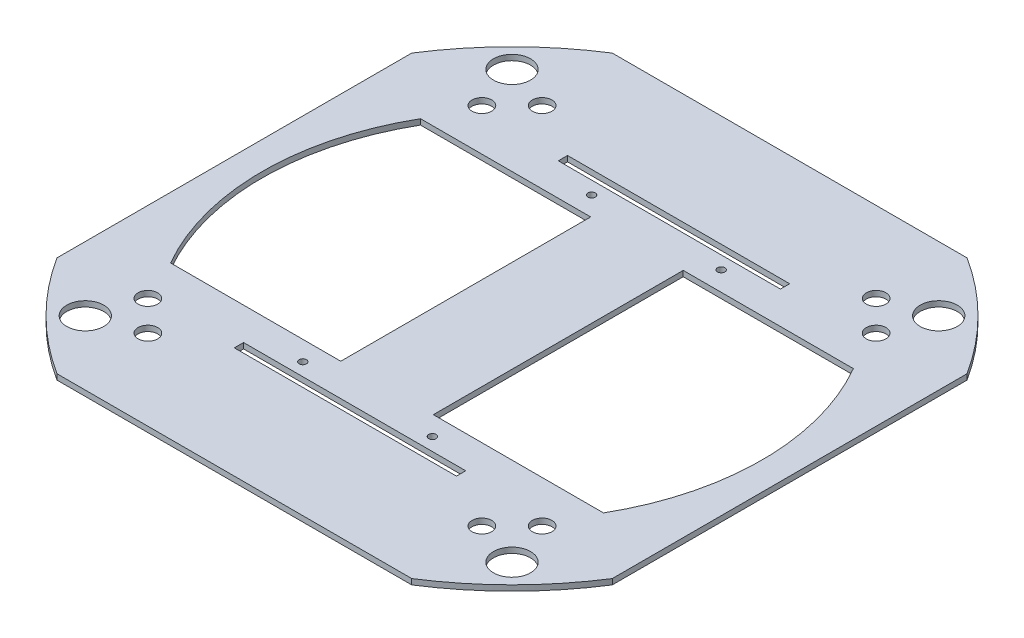
SolidWorks part; units mm, degrees
material "Hexcel AS4C (3000 丝)"
ref_plane "Front" through (0, 0, 0) normal (0, 0, 1) x (1, 0, 0)
ref_plane "Top" through (0, 0, 0) normal (0, 1, 0) x (1, 0, 0)
ref_plane "Right" through (0, 0, 0) normal (1, 0, 0) x (0, 0, -1)
sketch "草图3" plane through (0, 0, 0) normal (0, 1, 0) x (1, 0, 0)
  line L0 (0, 0) -> (125.865, 125.865) construction
  line L1 (0, 0) -> (-125.865, -125.865) construction
  line L2 (0, 0) -> (-125.865, 125.865) construction
  line L3 (0, 0) -> (125.865, -125.865) construction
  line L4 (0, 67.5) -> (0, 0) construction
  line L5 (0, 0) -> (0, 33.75) construction
  line L6 (0, 33.75) -> (25, 33.75) construction
  line L7 (0, 33.75) -> (-25, 33.75) construction
  line L8 (-25, 33.75) -> (-25, -67.5)
  line L9 (-25, 33.75) -> (-25, 67.5)
  line L10 (25, 33.75) -> (25, 67.5)
  line L11 (25, 33.75) -> (25, -67.5)
  line L27 (-135, 0) -> (0, 0) construction
  line L28 (0, 0) -> (-67.5, 0) construction
  line L29 (-67.5, 0) -> (0, 0) construction
  line L30 (0, 0) -> (135, 0) construction
  line L31 (135, 0) -> (67.5, 0) construction
  line L32 (0, -135) -> (0, 0) construction
  line L33 (0, 0) -> (0, 135) construction
  line L34 (0, 135) -> (0, 67.5) construction
  line L35 (0, 67.5) -> (0, 0) construction
  line L36 (0, 0) -> (0, -67.5) construction
  line L37 (0, -67.5) -> (0, -135) construction
  line L38 (25, 67.5) -> (116.9134, 67.5)
  line L39 (-25, 67.5) -> (-116.9134, 67.5)
  line L40 (25, -67.5) -> (116.9134, -67.5)
  line L41 (-25, -67.5) -> (-116.9134, -67.5)
  arc A0 (-116.9134, 67.5) -> (-116.9134, -67.5) centre (0, 0) ccw
  arc A5 (116.9134, -67.5) -> (116.9134, 67.5) centre (0, 0) ccw
  circle A6 centre (0, 0) radius 178
  point P36 (0, 0)
extrude "凸台-拉伸3" add sketch "草图3" along normal blind 3
sketch "草图4" plane through (0, 3, 0) normal (0, 1, 0) x (1, 0, 0)
  line L0 (-115.2584, -115.2584) -> (-125.865, -125.865) construction
  line L1 (125.865, 125.865) -> (115.2584, 115.2584) construction
  line L2 (-125.865, -125.865) -> (-95.8738, -95.8738) construction
  line L3 (-95.8738, -95.8738) -> (-90.2169, -101.5306) construction
  line L4 (-90.2169, -101.5306) -> (-95.1667, -106.4804) construction
  line L5 (-95.1667, -106.4804) -> (-90.2169, -111.4301) construction
  line L6 (-90.2169, -111.4301) -> (-90.2169, -101.5306) construction
  line L7 (-90.2169, -101.5306) -> (-90.2169, -106.4804) construction
  line L8 (-90.2169, -106.4804) -> (-95.1667, -106.4804) construction
  line L9 (-125.865, 125.865) -> (-95.8738, 95.8738) construction
  line L10 (125.865, 125.865) -> (95.8738, 95.8738) construction
  line L11 (125.865, -125.865) -> (95.8738, -95.8738) construction
  circle A0 centre (0, 0) radius 178 construction
  circle A1 centre (115.2584, 115.2584) radius 10
  circle A2 centre (115.2584, -115.2584) radius 10
  circle A3 centre (-115.2584, -115.2584) radius 10
  circle A4 centre (-115.2584, 115.2584) radius 10
  circle A5 centre (-90.2169, -106.4804) radius 5.3
  circle A6 centre (-106.4804, -90.2169) radius 5.3
  circle A7 centre (-106.4804, 90.2169) radius 5.3
  circle A8 centre (-90.2169, 106.4804) radius 5.3
  circle A9 centre (90.2169, 106.4804) radius 5.3
  circle A10 centre (106.4804, 90.2169) radius 5.3
  circle A11 centre (106.4804, -90.2169) radius 5.3
  circle A12 centre (90.2169, -106.4804) radius 5.3
  point P16 (0, 0)
  point P43 (0, 0)
  dimension "D1" = 4
extrude "切除-拉伸1" cut sketch "草图4" against normal blind 10
sketch "草图5" plane through (0, 3, 0) normal (0, 1, 0) x (1, 0, 0)
  line L0 (0, 0) -> (150, 0) construction
  line L1 (150, 0) -> (150, 95.8332) construction
  line L2 (0, 0) -> (0, 150) construction
  line L3 (0, 150) -> (95.8332, 150) construction
  line L4 (95.8332, 150) -> (0, 150)
  line L5 (0, 150) -> (-95.8332, 150)
  line L6 (150, 95.8332) -> (150, 0)
  line L7 (150, 0) -> (150, -95.8332)
  line L8 (95.8332, -150) -> (0, -150)
  line L9 (0, -150) -> (-95.8332, -150)
  line L10 (-150, 0) -> (-150, -95.8332)
  line L11 (-150, 95.8332) -> (-150, 0)
  circle A0 centre (0, 0) radius 178 construction
  arc A1 (-150, 95.8332) -> (-150, -95.8332) centre (0, 0) ccw
  arc A2 (150, -95.8332) -> (150, 95.8332) centre (0, 0) ccw
  arc A3 (-95.8332, -150) -> (95.8332, -150) centre (0, 0) ccw
  arc A4 (95.8332, 150) -> (-95.8332, 150) centre (0, 0) ccw
extrude "切除-拉伸2" cut sketch "草图5" against normal blind 10
sketch "草图6" plane through (0, 3, 0) normal (0, 1, 0) x (1, 0, 0)
  line L0 (0, -150) -> (0, -85) construction
  line L1 (95.8332, -150) -> (-95.8332, -150) construction
  line L2 (0, -85) -> (60, -85) construction
  line L3 (60, -85) -> (60, -90) construction
  line L4 (60, -90) -> (-60, -90) construction
  line L5 (-60, -90) -> (-60, -85) construction
  line L6 (-60, -85) -> (0, -85) construction
  line L7 (0, 0) -> (0, -78) construction
  line L8 (0, 0) -> (0, 78) construction
  line L9 (0, -78) -> (35, -78) construction
  line L10 (-60, -85) -> (60, -85)
  line L11 (60, -85) -> (60, -90)
  line L12 (60, -90) -> (-60, -90)
  line L13 (-60, -90) -> (-60, -85)
  line L14 (0, 0) -> (20.3938, 0) construction
  line L15 (-60, 90) -> (-60, 85)
  line L16 (60, 85) -> (60, 90)
  line L17 (-60, 85) -> (60, 85)
  line L18 (60, 90) -> (-60, 90)
  circle A0 centre (35, -78) radius 2
  circle A1 centre (-35, -78) radius 2
  circle A2 centre (-35, 78) radius 2
  circle A3 centre (35, 78) radius 2
extrude "切除-拉伸3" cut sketch "草图6" against normal blind 10
